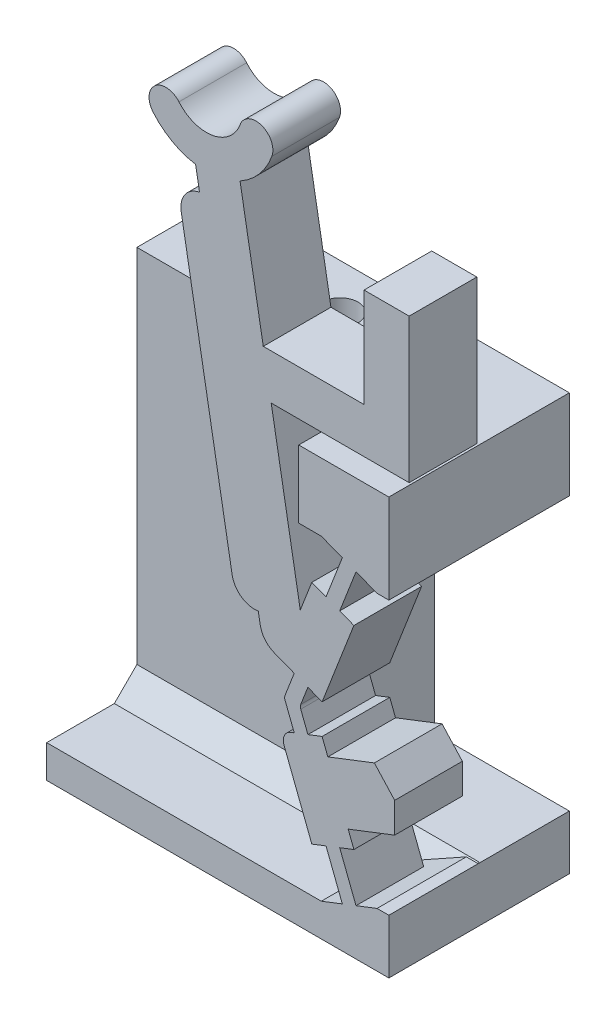
SolidWorks part; units mm, degrees
material "Nylon 6/12"
ref_plane "Front Plane" through (0, 0, 0) normal (0, 0, 1) x (1, 0, 0)
ref_plane "Top Plane" through (0, 0, 0) normal (0, 1, 0) x (1, 0, 0)
ref_plane "Right Plane" through (0, 0, 0) normal (1, 0, 0) x (0, 0, -1)
sketch "Sketch-SkeletonConfigUp" plane through (0, 0, 0) normal (0, 0, 1) x (1, 0, 0)
  line L0 (0, 0) -> (0, -50000) construction
  line L1 (-1.4217, 8.457) -> (-1.4217, 0) construction
  line L3 (0.7468, 14.0514) -> (-1.4217, 8.457) construction
  line L4 (-1.4217, 8.457) -> (0.7468, 2.8626) construction
  line L5 (0.7468, 14.0514) -> (2.1074, 19.3343) construction
  line L6 (-1.4217, 8.457) -> (-5.2203, 30) construction
  line L9 (0.7468, 14.0514) -> (0.7468, 2.8626) construction
  line L10 (0.7468, 2.8626) -> (0.7468, 0) construction
  line L11 (0, 0) -> (0.7468, 0) construction
  line L12 (0.7468, 0) -> (0, 0) construction
  dimension "D7" = 5.4552
  dimension "D10" = 6.745
  dimension "D3" = 2.1685
  dimension "D9" = 10
  dimension "D13" = 11.1888
  dimension "D14" = 30
  dimension "D5" = 10
  dimension "D2" = 21.8753
  dimension "D4" = 6
sketch "Sketch-SkeletonConfigDown" plane through (0, 0, 0) normal (0, 0, 1) x (1, 0, 0)
  line L0 (0, 0) -> (0, -50000) construction
  line L1 (0.7468, 14.0514) -> (0.7468, 2.8626) construction
  line L2 (5.9945, 14.5439) -> (0.7468, 14.0514) construction
  line L3 (0.7468, 14.0514) -> (2.9153, 8.457) construction
  line L4 (2.9153, 8.457) -> (0.7468, 2.8626) construction
  line L5 (0.7468, 14.0514) -> (-1.8086, 18.8711) construction
  line L6 (2.9153, 8.457) -> (-14.411, 21.8109) construction
  line L7 (0.7468, 2.8626) -> (5.9945, 14.5439) construction
  line L8 (-387.6937, -861.8102) -> (5.9945, 14.5439) construction
  line L10 (-1.4217, 8.457) -> (0.7468, 2.8626) construction
  line L11 (0.7468, 14.0514) -> (-1.4217, 8.457) construction
  line L12 (-1.4217, 8.457) -> (-5.2203, 30) construction
  line L13 (0.7468, 14.0514) -> (2.1074, 19.3343) construction
  dimension "D10" = 6.745
  dimension "D4" = 5.2707
  dimension "D5" = 119.553
  dimension "D2" = 52.378
  dimension "D3" = 31.19
ref_plane "Plane-Cam Base" through (3.8672, 0, 0) normal (1, 0, 0) x (0, 0, -1)
ref_plane "Plane-Down-to-Up Derailleur Clearance" through (1.3672, 0, 0) normal (1, 0, 0) x (0, 0, -1)
ref_plane "Plane-Cam Cavity Roof" through (-0.1328, 0, 0) normal (1, 0, 0) x (0, 0, -1)
sketch "Sketch-SwitchBossUp" plane through (0, 0, 0) normal (0, 0, 1) x (1, 0, 0)
  line L8 (-5.6979, 26.9497) -> (-5.5242, 25.9649)
  line L9 (-1.4217, 8.457) -> (-5.2203, 30) construction
  line L15 (-1.3272, 7.3139) -> (-0.7211, 7.5489) construction
  line L16 (-1.4217, 8.457) -> (0.7468, 2.8626) construction
  line L19 (0.0824, 13.2365) -> (0.6884, 13.0016) construction
  line L22 (0.8052, 15.1013) -> (1.4113, 14.8664) construction
  line L23 (-1.3272, 9.6001) -> (-1.9566, 9.8441)
  line L32 (1.0498, 2.9801) -> (0.4438, 2.7452) construction
  line L40 (-1.7703, 8.457) -> (-1.0732, 8.457) construction
  line L66 (-5.2203, 27.8193) -> (-5.2203, 50027.8193) construction
  line L74 (-4.078, 12.0039) -> (-6.3354, 24.8064)
  line L81 (2.3437, 2.4091) -> (2.8672, 2.4091)
  line L82 (-5.6111, 26.4573) -> (-3.6415, 26.8046) construction
  line L88 (-0.1116, 18.4627) -> (2.8672, 18.4627)
  line L92 (0.613, 5.9746) -> (-1.2518, 5.2518) construction
  line L95 (-2.3469, 19.4627) -> (3.7672, 19.4627)
  line L96 (2.8672, 14.505) -> (2.8672, 18.4627)
  line L97 (3.7672, 19.4627) -> (3.7672, 25.8576)
  line L101 (-1.0242, 7.4314) -> (-1.4217, 8.457) construction
  line L103 (-5.2203, 30) -> (-3.0238, 29.2005) construction
  line L107 (-1.3272, 9.6001) -> (-0.7211, 9.3652) construction
  line L109 (-5.2203, 30) -> (-7.011, 28.4975) construction
  line L114 (-0.0918, 7.7928) -> (-0.7211, 7.5489)
  line L117 (2.8672, 0) -> (-0.1272, 0)
  line L121 (0.7468, 0) -> (0, 0) construction
  line L122 (0.8052, 1.8128) -> (-0.1272, 1.4513)
  line L123 (1.4113, 2.0477) -> (2.3437, 2.4091)
  line L125 (2.8672, 2.4091) -> (2.8672, 0)
  line L127 (-0.7211, 9.3652) -> (-0.0918, 9.1213)
  line L133 (0.4438, 14.1689) -> (1.0498, 13.934) construction
  line L134 (-0.0918, 9.1213) -> (1.3178, 12.7576)
  line L135 (0.6884, 13.0016) -> (1.3178, 12.7576)
  line L142 (-0.1272, 1.4513) -> (-0.1272, 0)
  line L151 (0.0824, 13.2365) -> (-0.547, 13.4805)
  line L152 (0.8052, 15.1013) -> (0.0824, 13.2365)
  line L153 (1.4113, 14.8664) -> (0.6884, 13.0016)
  line L169 (0.0824, 3.6776) -> (0.8052, 1.8128)
  line L170 (1.4113, 2.0477) -> (0.6884, 3.9125)
  line L177 (0.6884, 3.9125) -> (0.0824, 3.6776) construction
  line L184 (-0.547, 13.4805) -> (-1.0591, 12.1594)
  line L191 (-1.3272, 7.3139) -> (-1.9566, 7.07)
  line L197 (3.7672, 25.8576) -> (1.7672, 25.8576)
  line L205 (1.7672, 25.8576) -> (1.7672, 21.4627)
  line L207 (12.0045, 16.6962) -> (12.0045, 16.6883) construction
  line L218 (0.6884, 3.9125) -> (1.3178, 4.1564)
  line L225 (-1.0591, 12.1594) -> (-2.3469, 19.4627)
  line L235 (-5.5242, 25.9649) -> (-2.7349, 10.1458) construction
  line L236 (-1.9566, 7.07) -> (-0.547, 3.4336)
  line L237 (-2.7349, 10.1458) -> (-2.9195, 11.1927)
  line L241 (-1.4217, 8.457) -> (-1.0242, 9.4827) construction
  line L242 (1.7672, 21.4627) -> (-2.6996, 21.4627)
  line L243 (-0.7211, 7.5489) -> (-1.0381, 8.3667)
  line L244 (-1.0381, 8.5474) -> (-0.7211, 9.3652)
  line L245 (-1.3272, 7.3139) -> (-1.7353, 8.3667)
  line L246 (-1.7353, 8.5474) -> (-1.3272, 9.6001)
  line L247 (-0.0918, 7.7928) -> (0.163, 7.1356)
  line L248 (0.8052, 1.8128) -> (1.4113, 2.0477) construction
  line L249 (0.0824, 3.6776) -> (-0.547, 3.4336)
  line L250 (-1.9566, 9.8441) -> (-0.547, 13.4805) construction
  line L251 (0.7468, 14.0514) -> (-1.4217, 8.457) construction
  line L252 (-1.2699, 11.6157) -> (0.5949, 10.8928) construction
  line L253 (-2.3469, 19.4627) -> (-2.6996, 21.4627) construction
  line L254 (-1.9566, 9.8441) -> (-2.7349, 10.1458)
  line L255 (0.8052, 15.1013) -> (-0.1272, 15.4627)
  line L256 (1.4113, 14.8664) -> (2.3437, 14.505)
  line L257 (2.3437, 14.505) -> (2.8672, 14.505)
  line L258 (-2.6996, 21.4627) -> (-3.7283, 27.297)
  line L259 (3.8672, -55) -> (3.8672, 55) construction
  line L260 (0.163, 7.1356) -> (2.225, 7.9349)
  line L261 (3.1252, 6.9484) -> (3.1252, 5.613)
  line L262 (3.1252, 5.613) -> (1.0631, 4.8136)
  line L263 (0.613, 5.9746) -> (3.1252, 6.9484) construction
  line L264 (1.0631, 4.8136) -> (0.613, 5.9746) construction
  line L265 (1.0631, 4.8136) -> (1.3178, 4.1564)
  line L266 (0.613, 5.9746) -> (0.163, 7.1356) construction
  line L267 (0.163, 7.1356) -> (0.613, 5.9746) construction
  line L268 (0.613, 5.9746) -> (1.0631, 4.8136) construction
  line L269 (0.163, 7.1356) -> (0.613, 5.9746) construction
  line L270 (0.613, 5.9746) -> (1.0631, 4.8136) construction
  line L271 (3.1252, 6.9484) -> (2.225, 7.9349)
  line L272 (1.8311, 5.6598) -> (3.8672, 4.8706) construction
  line L273 (2.9153, 8.457) -> (0.7468, 2.8626) construction
  line L274 (-0.3194, 5.6132) -> (2.225, 7.9349) construction
  line L275 (-0.3194, 5.6132) -> (3.8672, 5.6132) construction
  line L276 (-0.1272, 15.4627) -> (-1.1272, 15.4627)
  line L277 (-1.1272, 15.4627) -> (-1.1272, 18.4627)
  line L278 (-1.1272, 18.4627) -> (-0.1116, 18.4627)
  arc A0 (-3.7283, 27.297) -> (-2.319, 28.944) centre (-5.2203, 30) ccw
  arc A1 (-5.6979, 26.9497) -> (-7.5855, 28.0154) centre (-5.2203, 30) cw
  arc A2 (-7.5855, 28.0154) -> (-6.4364, 28.9796) centre (-7.011, 28.4975) cw
  arc A3 (-2.319, 28.944) -> (-3.7286, 29.457) centre (-3.0238, 29.2005) ccw
  arc A4 (-6.4364, 28.9796) -> (-3.7286, 29.457) centre (-5.2203, 30) ccw
  arc A19 (-6.3354, 24.8064) -> (-5.5242, 25.9649) centre (-5.3506, 24.98) cw
  circle A28 centre (-5.2203, 30) radius 2.3375 construction
  arc A30 (-4.078, 12.0039) -> (-2.9195, 11.1927) centre (-3.0932, 12.1775) ccw
  arc A31 (-1.0381, 8.3667) -> (-1.0381, 8.5474) centre (-0.805, 8.457) cw
  arc A32 (-1.7353, 8.3667) -> (-1.7353, 8.5474) centre (-1.5022, 8.457) cw
  point P5 (-4.6263, 26.6309)
  point P6 (-0.3194, 5.6132)
  point P45 (-0.3375, 11.2542)
  point P66 (4.5811, 6.2164)
  point P165 (0.7468, 14.0514)
  dimension "D23" = 1.5875
  dimension "D24" = 0.75
  dimension "D21" = 0.25
  dimension "D8" = 0.65
  dimension "D27" = 0.65
  dimension "D26" = 2
  dimension "D3" = 1.1
  dimension "D5" = 1.1
  dimension "D16" = 2
  dimension "D28" = 2
  dimension "D29" = 2
  dimension "D30" = 1
  dimension "D31" = 15
  dimension "D4" = 1.4169
  dimension "D6" = 0.65
  dimension "D7" = 2
  dimension "D11" = 1
  dimension "D10" = 1
  dimension "D9" = 0
  dimension "D12" = 60
  dimension "D13" = 60
  dimension "D14" = 2
  dimension "D15" = 1
  dimension "D17" = 2
  dimension "D19" = 0.1
  dimension "D22" = 42.38
  dimension "D18" = 3
  dimension "D25" = 1
  dimension "D32" = 1
  dimension "D20" = 1
extrude "Boss-Switch Body" add sketch "Sketch-SwitchBossUp" along normal blind 3
sketch "Sketch1" plane through (0, 0, 0) normal (0, 0, -1) x (-1, 0, 0)
  line L0 (-2.8672, 2.4091) -> (0.1272, 2.4091)
  line L1 (-2.8672, 0) -> (0.1272, 0)
  line L2 (-2.8672, 0) -> (-2.8672, 2.4091)
  line L4 (0.1272, 0) -> (0.1272, 2.4091)
  line L5 (1.1272, 14.505) -> (-2.8672, 14.505)
  line L10 (-2.8672, 14.505) -> (-2.8672, 18.4627)
  line L12 (-2.8672, 18.4627) -> (1.1272, 18.4627)
  line L14 (1.1272, 18.4627) -> (1.1272, 14.505)
  line L20 (-2.3437, 2.4091) -> (-2.8672, 2.4091) construction
  line L22 (-2.8672, 2.4091) -> (-2.3437, 2.4091) construction
  line L31 (0.1272, 0) -> (-2.8672, 0) construction
  line L32 (0.1272, 1.4513) -> (0.1272, 0) construction
extrude "Boss-Flange Width" add sketch "Sketch1" along normal blind 5
ref_plane "Plane-Sta2Sit Groove" through (-5.2203, 0, 0) normal (1, 0, 0) x (0, 0, -1)
ref_plane "Plane-Cam Outer Surface" through (-17.3003, 0, 0) normal (1, 0, 0) x (0, 0, -1)
ref_plane "Plane-FlangeTop" through (-12.3003, 0, 0) normal (1, 0, 0) x (0, 0, -1)
sketch "Sketch2" plane through (-12.3003, 0, 0) normal (1, 0, 0) x (0, 0, -1)
  line L0 (5, 18.4627) -> (-3, 18.4627) construction
  line L1 (5, 14.505) -> (1, 14.505)
  line L2 (5, 14.505) -> (5, 18.4627)
  line L3 (5, 18.4627) -> (1, 18.4627)
  line L4 (1, 14.505) -> (1, 18.4627)
  line L5 (5, 14.505) -> (-3, 14.505) construction
  line L11 (5, 1.4513) -> (-3, 1.4513)
  line L12 (5, 1.4513) -> (5, 0)
  line L13 (5, 0) -> (-3, 0)
  line L14 (-3, 1.4513) -> (-3, 0)
  line L15 (0, 8.457) -> (0, 30) construction
  line L16 (-3, 1.4513) -> (-3, 0) construction
  line L17 (5, 2.4091) -> (5, 0) construction
  line L19 (-3, 1.4513) -> (0, 1.4513) construction
  dimension "D1" = 1
extrude "Boss-Flange Height" add sketch "Sketch2" along normal up to surface (12.1731 mm away) up to face at (-0.1272, 1.2868, -0.6667)
sketch "Sketch17" plane through (0, 1.4513, 0) normal (0, -1, 0) x (1, 0, 0)
  line L0 (2.8672, -5) -> (-12.3003, -5)
  line L1 (2.8672, -5) -> (-12.3003, -5) construction
  line L2 (-12.3003, -5) -> (-12.3003, -1)
  line L3 (-12.3003, -1) -> (2.8672, -1)
  line L4 (2.8672, -1) -> (2.8672, -5)
  line L5 (-12.3003, -1) -> (-12.3003, -5) construction
  line L7 (-1.1272, -1) -> (-12.3003, -1) construction
extrude "Boss-Flange Support" add sketch "Sketch17" against normal up to surface (13.0536 mm away) up to face at (-1.4588, 14.505, -0.6)
sketch "Sketch27" plane through (0, 0, 0) normal (0, 0, 1) x (1, 0, 0)
  line L1 (-0.1272, 15.4627) -> (2.3437, 14.505)
  line L2 (2.3437, 14.505) -> (-1.1272, 14.505)
  line L3 (-1.1272, 14.505) -> (-1.1272, 15.4627)
  line L4 (-1.1272, 15.4627) -> (-0.1272, 15.4627)
  line L6 (-1.1272, 14.505) -> (2.8672, 14.505) construction
  line L7 (2.3437, 14.505) -> (1.2712, 14.505) construction
  line L8 (2.3437, 2.4091) -> (-0.1272, 2.4091)
  line L9 (-0.1272, 2.4091) -> (-0.1272, 1.4513)
  line L10 (-0.1272, 1.4513) -> (2.3437, 2.4091)
extrude "Cut-Wall Gap" cut sketch "Sketch27" against normal up to surface (1 mm away) up to face at (-2.6719, 9.207, -1)
ref_plane "Plane-Tap Depth" through (0, 13.4627, 0) normal (0, 1, 0) x (1, 0, 0)
sketch "Sketch-HolePositions" plane through (0, 0, 0) normal (0, -1, 0) x (1, 0, 0)
  line L0 (-12.3003, -3) -> (2.8672, -3) construction
  line L1 (2.8672, -5) -> (-12.3003, -5) construction
  line L2 (2.8672, -5) -> (2.8672, 3) construction
  line L4 (-12.3003, -22.2167) -> (-12.3003, 22.2167) construction
  point P6 (-9.3003, -3)
  point P7 (-5.3003, -3)
  dimension "D1" = 3
  dimension "D2" = 4
  dimension "D3" = 2
sketch "Sketch6" plane through (0, 0, 0) normal (0, -1, 0) x (-1, 0, 0)
  point P0 (9.3003, 3)
  point P3 (5.3003, 3)
hole_wizard "Tap Drill for M2x0.4 Tap1" positions "Sketch6" profile "Sketch5" hole size "M2x0.4" standard "ANSI Metric" end condition through all
sketch "Sketch5" plane through (-9.3003, 0, -3) normal (1, 0, 0) x (0, 0, -1)
  line L0 (0, 0) -> (0, 29.9505)
  line L1 (0, 29.9505) -> (0.8, 29.9505)
  line L2 (0.8, 29.9505) -> (0.8, 0)
  line L5 (0.8, 0) -> (0, 0)
  line L11 (0, -6.35) -> (0, 107.95) construction
  dimension "Thru Hole Dia." = 1.6
  dimension "Thru Hole Depth" = 29.9505
sketch "Sketch9" plane through (0, 0, 0) normal (0, -1, 0) x (1, 0, 0)
  point P0 (-9.3003, -3)
  point P3 (-5.3003, -3)
hole_wizard "M2 Clearance Hole2" positions "Sketch9" profile "Sketch8" hole size "M2" standard "ANSI Metric"
sketch "Sketch8" plane through (-9.3003, 0, -3) normal (1, 0, 0) x (0, 0, -1)
  line L0 (0, 0) -> (0, 14.1838)
  line L1 (0, 14.1838) -> (1.2, 13.4627)
  line L2 (1.2, 13.4627) -> (1.2, 0)
  line L5 (1.2, 0) -> (0, 0)
  line L10 (0, 14.1838) -> (-1.2, 13.4627) construction
  line L11 (0, -6.35) -> (0, 107.95) construction
  dimension "Hole Dia." = 2.4
  dimension "Hole Depth" = 13.4627
  dimension "Drill Angle" = 118
sketch "Sketch-Measurements for Derailleur Ramps" [suppressed] plane through (0, 0, 0) normal (0, 0, 1) x (1, 0, 0)
  line L0 (2.8784, 16.9852) -> (4.2265, 19.8331)
  line L1 (3.5524, 18.4092) -> (3.0492, 18.6474)
  line L2 (1.9779, 11.0613) -> (4.4465, 28.5428) construction
  line L3 (3.0492, 18.6474) -> (-4.0642, 13.8428)
  line L4 (7.1843, 11.0614) -> (-9.9544, 15.2993) construction
  line L5 (3.0492, 18.6474) -> (2.1536, 12.3053)
  line L6 (2.1536, 12.3053) -> (-4.0642, 13.8428)
  line L7 (-0.5075, 16.2451) -> (-0.5075, 18.6474)
  line L8 (-0.5075, 18.6474) -> (3.0492, 18.6474)
  line L9 (7.1843, 11.0614) -> (1.9779, 11.0613)
  line L10 (5.8827, 8.6389) -> (3.2795, 8.6389)
  line L12 (7.1843, 11.0614) -> (4.5811, 6.2164) construction
  line L13 (4.5811, 8.6389) -> (4.5811, 8.7912)
  line L14 (4.5811, 6.2164) -> (5.8827, 8.6389)
  line L15 (1.9779, 11.0613) -> (4.5811, 6.2164) construction
  line L16 (3.2795, 8.6389) -> (4.5811, 6.2164)
  line L17 (5.8827, 8.6389) -> (5.8827, 8.7912)
  dimension "D1" = 3.5567
  dimension "D2" = 1.3016
sketch "Sketch12" [suppressed] plane through (0, 23.1883, 0) normal (0, 1, 0) x (1, 0, 0)
  line L0 (10.0045, 0) -> (12.0045, -3)
  line L1 (12.0045, -3) -> (12.0045, 0)
  line L2 (12.0045, 0) -> (10.0045, 0)
extrude "Cut-Up-to-Down Cantilever Slope" [suppressed] cut sketch "Sketch12" against normal up to next
ref_plane "Plane1" [suppressed] through (0, 6.9404, 0) normal (0, 1, 0) x (1, 0, 0)
sketch "Sketch-Derailleur Location" [suppressed] plane through (0, 6.9404, 0) normal (0, 1, 0) x (1, 0, 0)
  line L0 (12.9465, 0) -> (12.9465, -3)
  line L1 (4.2399, -3) -> (3.2603, -3) construction
  line L2 (-119237.4187, 0) -> (9.8143, 0) construction
  point P0 (12.9465, 0)
  point P8 (12.9465, -1.5)
ref_plane "Plane-Cantilever Cut" [suppressed] through (7.0848, 8.5204, -1.9058) normal (-0.6301, -0.7578, 0.1695) x (-0.7765, 0.6151, -0.1368)
sketch "Sketch14" [suppressed] plane through (7.0848, 8.5204, -1.9058) normal (-0.6301, -0.7578, 0.1695) x (-0.7765, 0.6151, -0.1368)
  line L0 (2.3023, -1.6911) -> (-0.3551, -1.6911)
  line L2 (2.3023, -4.3362) -> (2.3023, -1.6911)
  line L3 (-0.3551, -1.6911) -> (-0.3551, -4.4608)
  line L5 (-0.3551, -4.4608) -> (1.0087, -5.0843)
  line L6 (1.0087, -5.0843) -> (2.3023, -4.3362)
extrude "Cut-Down-to-Up Cantilever Slope" [suppressed] cut sketch "Sketch14" against normal up to next
ref_plane "Plane-Symmetry Plane" through (0, 0, 1.5) normal (0, 0, 1) x (1, 0, 0)
sketch "Sketch-Cable Center Point" plane through (0, 0, 1.5) normal (0, 0, 1) x (1, 0, 0)
  line L0 (-5.2203, 30) -> (-5.0825, 29.2183)
  line L1 (-1.4217, 8.457) -> (-5.2203, 30) construction
  point P0 (-5.2203, 30)
  dimension "D1" = 0.7937
sketch "Sketch28" plane through (0, 0, -1) normal (0, 0, 1) x (1, 0, 0)
  line L0 (2.8672, 14.505) -> (2.8672, 2.4091)
  line L1 (2.3437, 2.4091) -> (2.8672, 2.4091) construction
  line L2 (2.8672, 14.505) -> (-3.1003, 14.505)
  line L3 (-3.1003, 14.505) -> (-3.1003, 2.4091)
  line L4 (-3.1003, 2.4091) -> (2.8672, 2.4091)
  line L6 (-6.5003, 13.4627) -> (-4.1003, 13.4627) construction
  line L7 (-6.5003, 13.4627) -> (-4.1003, 13.4627) construction
  dimension "D1" = 1
chamfer "Chamfer-Flange Support" [suppressed] distance 1.5 angle 45
chamfer "Chamfer-Flange Support 3" distance 1 angle 45 1 edges at (-6.2138, 1.4513, -1)
fillet "Fillet1" radius 1 1 edges at (-2.7349, 10.1458, 1.5)
fillet "Fillet2" radius 0.5 1 edges at (-1.9566, 7.07, 1.5)
extrude "Cut-Print Support Clearance" cut sketch "Sketch28" against normal through all
equation "\"axle-diameter\"=2"
equation "\"switch-thickness\"=12"
equation "\"base-width\"=4.0"
equation "\"axle-bushing-radius\"=3"
equation "\"clearance\"= 0.25"
equation "\"arm-width\"=1.5"
equation "\"min-diameter\"=70"
equation "\"alpha\"=143.6120"
equation "\"gamma\"=119.5526"
equation "\"delta\"=145.9637"
equation "\"epsilon\"=6.7452"
equation "\"l_AB\"=8.8212"
equation "\"l_AC\"=4.4914"
equation "\"l_BD\"=5.2707"
equation "\"l_CD\"=3.8848"
equation "\"l_CE\"=10.9181"
equation "\"l_DF\"=5.4552"
equation "\"l_OA\"=7.7221"
equation "\"D7@Sketch-SkeletonConfigUp\" = \"l_DF\""
equation "\"D_groove\"=3.175"
equation "\"D5@Sketch-SkeletonConfigDown\" = \"gamma\""
equation "\"D4@Sketch-SkeletonConfigDown\" = \"l_BD\""
equation "\"hinge_length\"=1.5"
equation "\"hinge_depth\"=0.25"
equation "\"D10@Sketch-SkeletonConfigUp\"=\"epsilon\""
equation "\"D10@Sketch-SkeletonConfigDown\"=\"epsilon\""
equation "\"EE_dx\"=8.9056"
equation "\"EE_dy\"=8.1898"
equation "\"r_groove\"=\"D_groove\"/2"
equation "\"t_wall\"=25.4/16"
equation "\"width_lower\"=\"D_groove\"+\"t_wall\""
equation "\"cable_to_bottom\"=30.6257"
equation "\"switch_EE-up_base_dy\"=24"
equation "\"switch_EE-down_base_dy\"=16"
equation "\"D_axle\"=25.4/8"
equation "\"D_up_to_down\"=16"
equation "\"D_down_to_up\"=25"
equation "\"t_cam_base\"=7.5"
equation "\"D23@Sketch-SwitchBossUp\"=\"D_groove\"/2"
equation "\"D1@Sketch-Cable Center Point\"=\"D_groove\"/4"
